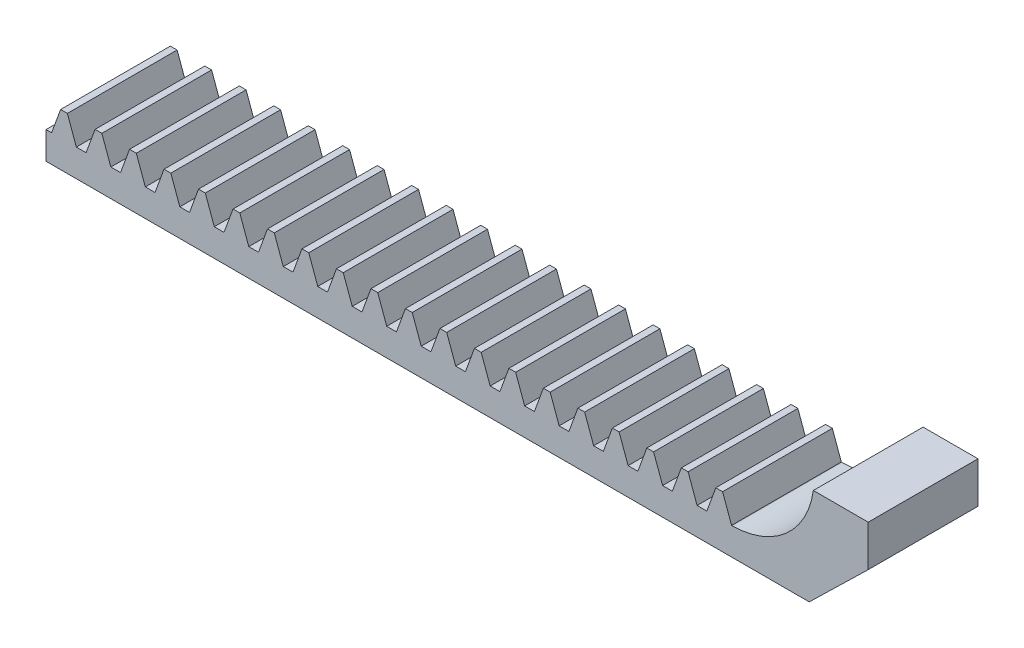
SolidWorks part; units mm, degrees
extrude "Blank" add sketch "BlankSke" against normal blind 8
sketch "BlankSke" plane through (0, 0, 0) normal (0, 0, 1) x (1, 0, 0)
  line L1 (0, 0) -> (60, 0)
  line L2 (0, 0) -> (0, 3.8)
  line L3 (0, 3.8) -> (60, 3.8)
  line L4 (60, 0) -> (60, 3.8)
  dimension "Length" = 60
  dimension "Blank_height" = 3.8
ref_plane "Plane1" through (0, 0, 0) normal (0, 0, 1) x (1, 0, 0)
ref_plane "Plane2" through (0, 0, 0) normal (0, 1, 0) x (1, 0, 0)
ref_plane "Plane3" through (0, 0, 0) normal (1, 0, 0) x (0, 0, -1)
other "Configuration Table"
sketch "HoldingSke" plane through (0, 0, 0) normal (0, 1, 0) x (1, 0, 0)
  line L0 (0, 0) -> (0.174, 1.2378)
  line L1 (-15, 0) -> (100, 0) construction
  line L2 (0, 0) -> (-2.1039, 2.3779)
  line L3 (0, 0) -> (-11.863, 4.5341)
  line L4 (0, 0) -> (7.8269, 3.6497)
  line L5 (0, 0) -> (-23.7986, -8.8762)
  line L6 (0, 0) -> (-10.5278, -7.1032)
  line L9 (-71.009, 38.7566) -> (-14.6274, 59.2778)
  line L10 (-76.2, 3.1779) -> (-73.2, 3.1779)
  line L11 (0, 0) -> (-8, 0)
  line L12 (-76.2, 101.6) -> (-76.17, 101.6)
  line L13 (24.9733, 27.94) -> (52.9518, 28.4284)
  line L14 (24.9733, 27.94) -> (24.9743, 27.94)
  line L15 (24.9733, 27.94) -> (100.4006, 29.5858)
  circle A0 centre (0, 0) radius 19.05
  circle A1 centre (0, 0) radius 1.5
  circle A2 centre (0, 0) radius 12.7
  dimension "MPH" = 3
  dimension "Diameter" = 38.1
  dimension "Num_teeth" = 25
  dimension "Pitch" = 1.25
  dimension "Show_teeth" = 998
  dimension "Thickness" = 12.7
  dimension "Ap" = 20
  dimension "Pitch_height" = 3
  dimension "Width" = 8
  dimension "Backlash" = 0.03
  dimension "Addendum_fac" = 1
  dimension "Dedendum_fac" = 1.25
  dimension "Clearance_fac" = 0.25
  dimension "Dedendum_add" = 0.001
  dimension "Length" = 60
  dimension "Module" = 0.8
sketch "TooCutSkeIll" plane through (0, 0, 0) normal (0, 0, 1) x (1, 0, 0)
  line L0 (-1.0018, 3.7789) -> (-0.4025, 2.1323)
  line L1 (-0.2136, 2) -> (0.2136, 2)
  line L2 (0.4025, 2.1323) -> (1.0018, 3.7789)
  line L3 (60, 3.8) -> (0, 3.8) construction
  line L4 (0, 0) -> (0, 64.897) construction
  line L5 (-13.208, 3) -> (12.954, 3) construction
  line L6 (0, 0) -> (60, 0) construction
  line L7 (0.7183, 3) -> (0.7183, 48.7463) construction
  line L8 (-0.7183, 3) -> (-0.7183, 48.7463) construction
  line L9 (1.0319, 3.8) -> (1.0319, 3.8254)
  line L10 (-1.0319, 3.8) -> (-1.0319, 3.8254)
  line L11 (-1.0319, 3.8254) -> (1.0319, 3.8254)
  arc A0 (0.2136, 2) -> (0.4025, 2.1323) centre (0.2136, 2.201) ccw
  arc A1 (-0.4025, 2.1323) -> (-0.2136, 2) centre (-0.2136, 2.201) ccw
  arc A2 (1.0319, 3.8) -> (1.0018, 3.7789) centre (1.0319, 3.768) ccw
  arc A3 (-1.0018, 3.7789) -> (-1.0319, 3.8) centre (-1.0319, 3.768) ccw
  dimension "Pitch_height" = 3
  dimension "Addendum_plus" = 0.8254
  dimension "Pressure_angle" = 20
  dimension "Gap_width" = 1.4366
  dimension "Dedendum" = 1
extrude "ToothCutIll" [suppressed] cut sketch "TooCutSkeIll" against normal through all
sketch "TooCutSkeSim" plane through (0, 0, 0) normal (0, 0, 1) x (1, 0, 0)
  line L0 (0.3543, 2) -> (-0.3543, 2)
  line L1 (1.0187, 3.8254) -> (0.3543, 2)
  line L2 (0, 17.4625) -> (0, 53.467) construction
  line L3 (1.0187, 3.8254) -> (-1.0187, 3.8254)
  line L6 (-1.0187, 3.8254) -> (-0.3543, 2)
  line L9 (-0.7183, 3) -> (0.7183, 3) construction
  line L10 (0, 0) -> (60, 0) construction
  line L11 (0.7183, 3) -> (0.7183, 53.467) construction
  line L12 (-0.7183, 3) -> (-0.7183, 53.467) construction
  dimension "Pitch_height" = 3
  dimension "Addendum_plus" = 0.8254
  dimension "Pressure_angle" = 20
  dimension "Gap_width" = 1.4366
  dimension "Dedendum" = 1
extrude "ToothCutSim" cut sketch "TooCutSkeSim" against normal through all
pattern_linear "TeethCuts" count 25 spacing 2.5133 along (1, 0, 0) of "ToothCutIll", "ToothCutSim"
sketch "草图1" plane through (0, 0, 0) normal (0, 0, 1) x (1, 0, 0)
  line L0 (60, 0) -> (65.6239, 0)
  line L1 (65.6239, 0) -> (69.9239, 4.1838)
  line L2 (69.9239, 4.1838) -> (69.9239, 7.1838)
  line L3 (69.9239, 7.1838) -> (65.9239, 7.1838)
  line L4 (60, 0) -> (60, 2)
  arc A0 (60, 2) -> (65.9239, 7.1838) centre (59.9797, 8) ccw
  dimension "D1" = 12
  dimension "D2" = 4.3
  dimension "D3" = 3
  dimension "D4" = 4
extrude "凸台-拉伸1" add sketch "草图1" against normal blind 8
sketch "草图2" plane through (0, 0, 0) normal (0, 0, 1) x (1, 0, 0)
  line L1 (0, 0) -> (10, 0)
  line L2 (0, 0) -> (0, 6.667)
  line L3 (0, 6.667) -> (10, 6.667)
  line L4 (10, 0) -> (10, 6.667)
  dimension "D1" = 10
extrude "切除-拉伸1" cut sketch "草图2" against normal blind 8
equation "' \"Module@HoldingSke\" = 6.35"
equation "' \"Num_teeth@HoldingSke\" = 12"
equation "' \"Ap@HoldingSke\" =  20"
equation "' \"Ap@HoldingSke\" = 20"
equation "' \"Width@HoldingSke\" = 0.25 * 25.4"
equation "' \"Show_teeth@HoldingSke\" = 500"
equation "' \"Backlash@HoldingSke\" = 0.009 * 25.4"
equation "' \"Addendum_fac@HoldingSke\" = 1.0"
equation "' \"Dedendum_fac@HoldingSke\" = 1.25"
equation "' \"Dedendum_add@HoldingSke\" = 0.00005 * 25.4"
equation "' \"Clearance_fac@HoldingSke\" = 0.25"
equation "' \"Pitch_height@HoldingSke\" = 1 * 25.4"
equation "' \"Length@HoldingSke\" = 4.71 * 25.4"
equation "\"Pitch@HoldingSke\" = 1 / \"Module@HoldingSke\""
equation "\"MPH@HoldingSke\" = \"Dedendum_fac@HoldingSke\" / \"Pitch@HoldingSke\" + 2 * \"Dedendum_add@HoldingSke\" + 0.002 * 25.4"
equation "\"MPH@HoldingSke\" = ((sgn( \"MPH@HoldingSke\" - \"Pitch_height@HoldingSke\")+1)*( \"MPH@HoldingSke\" - \"Pitch_height@HoldingSke\"))/2 + \"Pitch_height@HoldingSke\""
equation "\"Blank_height@BlankSke\" = \"Pitch_height@HoldingSke\" + \"Addendum_fac@HoldingSke\"  / \"Pitch@HoldingSke\" "
equation "\"Length@BlankSke\" =  \"Length@HoldingSke\""
equation "\"Face_width@Blank\" = \"Width@HoldingSke\""
equation "\"Pressure_angle@TooCutSkeIll\" = \"Ap@HoldingSke\""
equation "\"Addendum_plus@TooCutSkeIll\" =  \"Addendum_fac@HoldingSke\"  / \"Pitch@HoldingSke\" + 0.001 *25.4"
equation "\"Dedendum@TooCutSkeIll\" = \"Dedendum_fac@HoldingSke\"  / \"Pitch@HoldingSke\""
equation "\"Pitch_height@TooCutSkeIll\" =  \"MPH@HoldingSke\""
equation "\"Gap_width@TooCutSkeIll\" = 3.14159265 / 2 / \"Pitch@HoldingSke\" + 6 * \"Backlash@HoldingSke\""
equation "\"Pressure_angle@TooCutSkeSim\" = \"Ap@HoldingSke\""
equation "\"Addendum_plus@TooCutSkeSim\" =  \"Addendum_fac@HoldingSke\"  / \"Pitch@HoldingSke\" + 0.001 * 25.4"
equation "\"Dedendum@TooCutSkeSim\" = \"Dedendum_fac@HoldingSke\"  / \"Pitch@HoldingSke\""
equation "\"Pitch_height@TooCutSkeSim\" =  \"MPH@HoldingSke\""
equation "\"Gap_width@TooCutSkeSim\" = 3.14159265 / 2 / \"Pitch@HoldingSke\" + 6 * \"Backlash@HoldingSke\""
equation "\"Root_fillet@TooCutSkeIll\" = \"Clearance_fac@HoldingSke\" / \"Pitch@HoldingSke\" + \"Dedendum_add@HoldingSke\""
equation "\"Break_rad@TooCutSkeIll\" = 0.02 / \"Pitch@HoldingSke\" * 2"
equation "\"Linear_pitch@TeethCuts\" = 3.14159265 / \"Pitch@HoldingSke\""
equation "\"Num_teeth@HoldingSke\" = int( ( \"Length@HoldingSke\" + 0 ) / (3.14159265 / \"Pitch@HoldingSke\")) + 0.9999  + 1"
equation " \"Num_teeth@TeethCuts\" = int( \"Show_teeth@HoldingSke\" ) + 1"
equation " \"Num_teeth@TeethCuts\" = ((sgn( \"Num_teeth@TeethCuts\" - \"Num_teeth@HoldingSke\" )-1)*( \"Num_teeth@TeethCuts\" - \"Num_teeth@HoldingSke\" ))/-2+ \"Num_teeth@HoldingSke\""
equation " \"Num_teeth@TeethCuts\" = ((sgn( \"Num_teeth@TeethCuts\" - 2.0)+1)*( \"Num_teeth@TeethCuts\" - 2.0))/2 +2.0"
